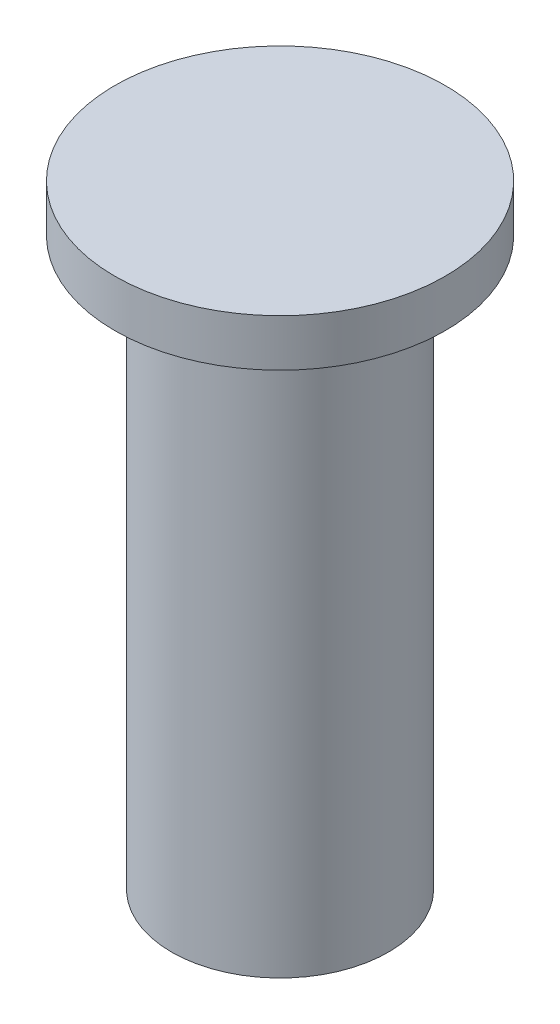
SolidWorks part; units mm, degrees
ref_plane "Front Plane" through (0, 0, 0) normal (0, 0, 1) x (1, 0, 0)
ref_plane "Top Plane" through (0, 0, 0) normal (0, 1, 0) x (1, 0, 0)
ref_plane "Right Plane" through (0, 0, 0) normal (1, 0, 0) x (0, 0, -1)
sketch "Sketch1" plane through (0, 0, 0) normal (0, 1, 0) x (1, 0, 0)
  circle A0 centre (0, 0) radius 2.3
  dimension "D1" = 4.6
extrude "main_body" add sketch "Sketch1" along normal blind 12
sketch "Sketch2" plane through (0, 12, 0) normal (0, 1, 0) x (1, 0, 0)
  circle A0 centre (0, 0) radius 3.5
  dimension "D1" = 7
extrude "pin_head" add sketch "Sketch2" along normal blind 1
